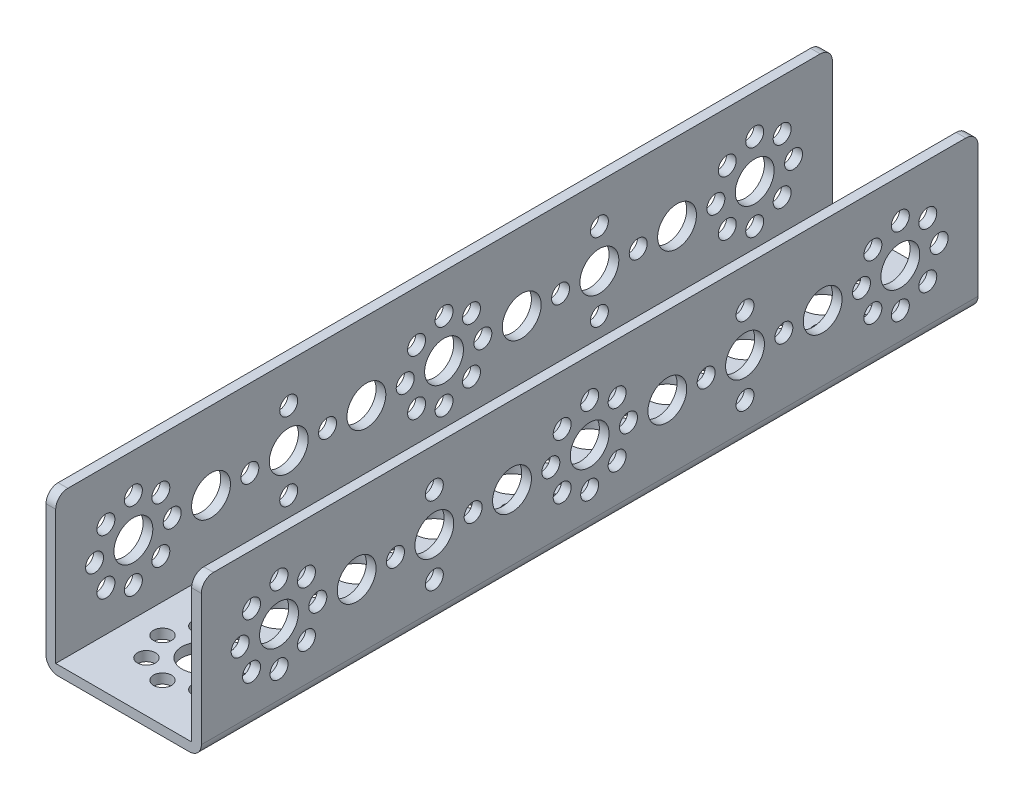
SolidWorks part; units mm, degrees
material "2024 Alloy"
ref_plane "Front Plane" through (0, 0, 0) normal (0, 0, 1) x (1, 0, 0)
ref_plane "Top Plane" through (0, 0, 0) normal (0, 1, 0) x (1, 0, 0)
ref_plane "Right Plane" through (0, 0, 0) normal (1, 0, 0) x (0, 0, -1)
ref_plane "Plane1" through (16, 0, 0) normal (1, 0, 0) x (0, 0, -1)
sketch "Sketch1" plane through (16, 0, 0) normal (1, 0, 0) x (0, 0, -1)
  line L0 (-16, 32) -> (-16, 0)
  line L1 (-16, 0) -> (144, 0)
  line L2 (144, 0) -> (144, 32)
  line L3 (144, 32) -> (-16, 32)
extrude "Boss-Extrude1" add sketch "Sketch1" against normal blind 32
sketch "Sketch2" plane through (0, 0, -144) normal (0, 0, -1) x (-1, 0, 0)
  line L0 (14, 32) -> (-14, 32)
  line L1 (-14, 32) -> (-14, 2)
  line L2 (-14, 2) -> (14, 2)
  line L3 (14, 2) -> (14, 32)
extrude "Cut-Extrude1" cut sketch "Sketch2" against normal through all
hole_wizard "Ø8.0 (8) Diameter Hole1" positions "Sketch4" profile "Sketch3" hole size "Ø8.0" standard "ANSI Metric"
sketch "Sketch4" plane through (-16, 0, 0) normal (-1, 0, 0) x (0, 0, 1)
  point P0 (-64, 16)
  point P1 (-128, 16)
  point P2 (-32, 16)
  point P3 (-96, 16)
  point P4 (-16, 16)
  point P5 (-48, 16)
  point P6 (-80, 16)
  point P7 (-112, 16)
  point P8 (0, 16)
sketch "Sketch3" plane through (-16, 16, -64) normal (0, 1, 0) x (0, 0, 1)
  line L0 (0, 0) -> (0, 2)
  line L1 (0, 2) -> (4, 2)
  line L2 (4, 2) -> (4, 0)
  line L5 (4, 0) -> (0, 0)
  line L11 (0, -6.35) -> (0, 107.95) construction
  dimension "Thru Hole Dia." = 8
  dimension "Thru Hole Depth" = 2
hole_wizard "Ø3.7 (3.7) Diameter Hole1" positions "Sketch6" profile "Sketch5" hole size "Ø3.7" standard "ANSI Metric"
sketch "Sketch6" plane through (-16, 0, 0) normal (-1, 0, 0) x (0, 0, 1)
  point P0 (0, 24)
  point P1 (0, 8)
  point P2 (-8, 16)
  point P3 (8, 16)
  point P4 (-5.6569, 21.6569)
  point P5 (5.6569, 21.6569)
  point P6 (5.6569, 10.3431)
  point P7 (-5.6569, 10.3431)
  point P8 (-64, 24)
  point P9 (-64, 8)
  point P10 (-72, 16)
  point P11 (-56, 16)
  point P12 (-69.6569, 21.6569)
  point P13 (-58.3431, 21.6569)
  point P14 (-58.3431, 10.3431)
  point P15 (-69.6569, 10.3431)
  point P16 (-128, 24)
  point P17 (-128, 8)
  point P18 (-136, 16)
  point P19 (-120, 16)
  point P20 (-133.6569, 21.6569)
  point P21 (-122.3431, 21.6569)
  point P22 (-122.3431, 10.3431)
  point P23 (-133.6569, 10.3431)
  point P24 (-32, 24)
  point P25 (-40, 16)
  point P26 (-32, 8)
  point P27 (-24, 16)
  point P28 (-96, 24)
  point P29 (-104, 16)
  point P30 (-96, 8)
  point P31 (-88, 16)
sketch "Sketch5" plane through (-16, 24, 0) normal (0, 1, 0) x (0, 0, 1)
  line L0 (0, 0) -> (0, 2)
  line L1 (0, 2) -> (1.85, 2)
  line L2 (1.85, 2) -> (1.85, 0)
  line L5 (1.85, 0) -> (0, 0)
  line L11 (0, -6.35) -> (0, 107.95) construction
  dimension "Thru Hole Dia." = 3.7
  dimension "Thru Hole Depth" = 2
hole_wizard "Ø3.7 (3.7) Diameter Hole2" positions "Sketch8" profile "Sketch7" hole size "Ø3.7" standard "ANSI Metric"
sketch "Sketch8" plane through (0, 0, 0) normal (0, -1, 0) x (-1, 0, 0)
  point P0 (8, 0)
  point P1 (5.6569, 5.6569)
  point P2 (0, 8)
  point P3 (-5.6569, 5.6569)
  point P4 (-8, 0)
  point P5 (-5.6569, -5.6569)
  point P6 (0, -8)
  point P7 (5.6569, -5.6569)
  point P8 (8, 64)
  point P9 (5.6569, 69.6569)
  point P10 (0, 72)
  point P11 (-5.6569, 69.6569)
  point P12 (-8, 64)
  point P13 (-5.6569, 58.3431)
  point P14 (0, 56)
  point P15 (5.6569, 58.3431)
  point P16 (8, 128)
  point P17 (5.6569, 133.6569)
  point P18 (0, 136)
  point P19 (-5.6569, 133.6569)
  point P20 (-8, 128)
  point P21 (-5.6569, 122.3431)
  point P22 (0, 120)
  point P23 (5.6569, 122.3431)
  point P24 (8, 32)
  point P25 (0, 40)
  point P26 (-8, 32)
  point P27 (0, 24)
  point P28 (8, 96)
  point P29 (0, 104)
  point P30 (-8, 96)
  point P31 (0, 88)
sketch "Sketch7" plane through (-8, 0, 0) normal (1, 0, 0) x (0, 0, -1)
  line L0 (0, 0) -> (0, 32)
  line L1 (0, 32) -> (1.85, 32)
  line L2 (1.85, 32) -> (1.85, 0)
  line L5 (1.85, 0) -> (0, 0)
  line L11 (0, -6.35) -> (0, 107.95) construction
  dimension "Thru Hole Dia." = 3.7
  dimension "Thru Hole Depth" = 32
hole_wizard "Ø8.0 (8) Diameter Hole2" positions "Sketch10" profile "Sketch9" hole size "Ø8.0" standard "ANSI Metric"
sketch "Sketch10" plane through (0, 0, 0) normal (0, -1, 0) x (-1, 0, 0)
  point P0 (0, 0)
  point P1 (0, 64)
  point P2 (0, 128)
  point P3 (0, 32)
  point P4 (0, 96)
  point P5 (0, 16)
  point P6 (0, 48)
  point P7 (0, 80)
  point P8 (0, 112)
sketch "Sketch9" plane through (0, 0, 0) normal (1, 0, 0) x (0, 0, -1)
  line L0 (0, 0) -> (0, 32)
  line L1 (0, 32) -> (4, 32)
  line L2 (4, 32) -> (4, 0)
  line L5 (4, 0) -> (0, 0)
  line L11 (0, -6.35) -> (0, 107.95) construction
  dimension "Thru Hole Dia." = 8
  dimension "Thru Hole Depth" = 32
hole_wizard "Ø8.0 (8) Diameter Hole3" positions "Sketch12" profile "Sketch11" hole size "Ø8.0" standard "ANSI Metric"
sketch "Sketch12" plane through (14, 0, 0) normal (-1, 0, 0) x (0, 0, 1)
  point P0 (-32, 16)
sketch "Sketch11" plane through (14, 16, -32) normal (0, 1, 0) x (0, 0, 1)
  line L0 (0, 0) -> (0, 2)
  line L1 (0, 2) -> (4, 2)
  line L2 (4, 2) -> (4, 0)
  line L5 (4, 0) -> (0, 0)
  line L11 (0, -6.35) -> (0, 107.95) construction
  dimension "Thru Hole Dia." = 8
  dimension "Thru Hole Depth" = 2
hole_wizard "Ø8.0 (8) Diameter Hole4" positions "Sketch14" profile "Sketch13" hole size "Ø8.0" standard "ANSI Metric"
sketch "Sketch14" plane through (16, 0, 0) normal (1, 0, 0) x (0, 0, -1)
  point P0 (64, 16)
  point P1 (128, 16)
  point P2 (96, 16)
  point P3 (16, 16)
  point P4 (48, 16)
  point P5 (80, 16)
  point P6 (112, 16)
  point P7 (0, 16)
sketch "Sketch13" plane through (16, 16, -64) normal (0, 1, 0) x (0, 0, -1)
  line L0 (0, 0) -> (0, 32)
  line L1 (0, 32) -> (4, 32)
  line L2 (4, 32) -> (4, 0)
  line L5 (4, 0) -> (0, 0)
  line L11 (0, -6.35) -> (0, 107.95) construction
  dimension "Thru Hole Dia." = 8
  dimension "Thru Hole Depth" = 32
hole_wizard "Ø3.7 (3.7) Diameter Hole3" positions "Sketch16" profile "Sketch15" hole size "Ø3.7" standard "ANSI Metric"
sketch "Sketch16" plane through (16, 0, 0) normal (1, 0, 0) x (0, 0, -1)
  point P0 (0, 24)
  point P1 (0, 8)
  point P2 (8, 16)
  point P3 (-8, 16)
  point P4 (5.6569, 21.6569)
  point P5 (-5.6569, 21.6569)
  point P6 (-5.6569, 10.3431)
  point P7 (5.6569, 10.3431)
  point P8 (64, 24)
  point P9 (64, 8)
  point P10 (72, 16)
  point P11 (56, 16)
  point P12 (69.6569, 21.6569)
  point P13 (58.3431, 21.6569)
  point P14 (58.3431, 10.3431)
  point P15 (69.6569, 10.3431)
  point P16 (128, 24)
  point P17 (128, 8)
  point P18 (136, 16)
  point P19 (120, 16)
  point P20 (133.6569, 21.6569)
  point P21 (122.3431, 21.6569)
  point P22 (122.3431, 10.3431)
  point P23 (133.6569, 10.3431)
  point P24 (32, 24)
  point P25 (40, 16)
  point P26 (32, 8)
  point P27 (24, 16)
  point P28 (96, 24)
  point P29 (104, 16)
  point P30 (96, 8)
  point P31 (88, 16)
sketch "Sketch15" plane through (16, 24, 0) normal (0, 1, 0) x (0, 0, -1)
  line L0 (0, 0) -> (0, 32)
  line L1 (0, 32) -> (1.85, 32)
  line L2 (1.85, 32) -> (1.85, 0)
  line L5 (1.85, 0) -> (0, 0)
  line L11 (0, -6.35) -> (0, 107.95) construction
  dimension "Thru Hole Dia." = 3.7
  dimension "Thru Hole Depth" = 32
fillet "Fillet1" radius 2.5 6 edges at (-16, 0, -64) (-15, 32, -144) (-15, 32, 16) (16, 0, -64) (15, 32, 16) (15, 32, -144)
